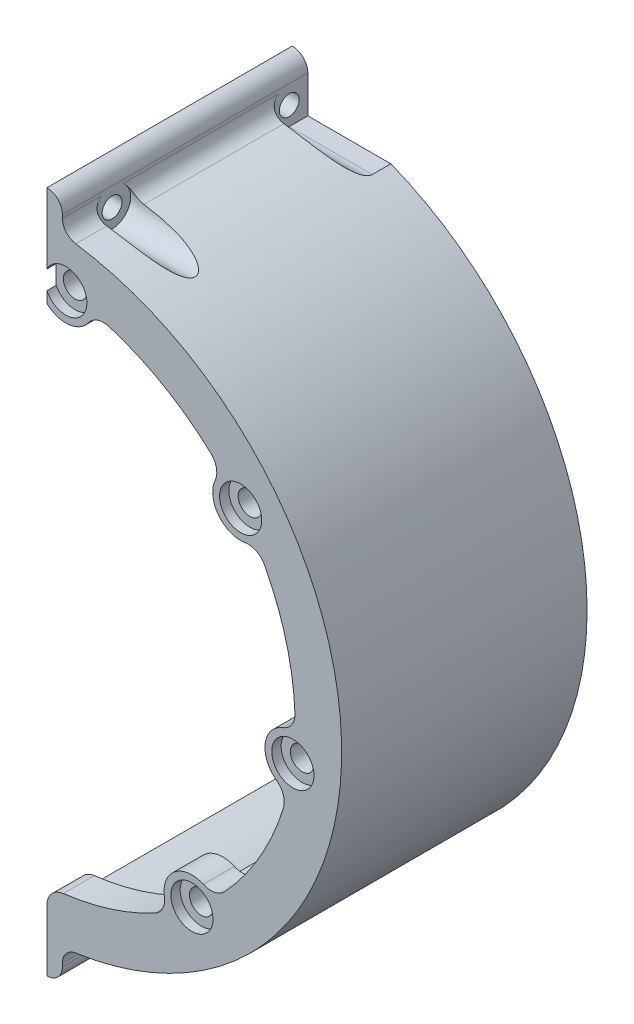
SolidWorks part; units mm, degrees
material "ABS"
ref_plane "前视基准面" through (0, 0, 0) normal (0, 0, 1) x (1, 0, 0)
ref_plane "上视基准面" through (0, 0, 0) normal (0, 1, 0) x (1, 0, 0)
ref_plane "右视基准面" through (0, 0, 0) normal (1, 0, 0) x (0, 0, -1)
sketch "草图1" plane through (0, 0, 0) normal (0, 0, 1) x (1, 0, 0)
  line L0 (0, 0) -> (0, 50)
  line L1 (0, 0) -> (0, -50)
  arc A0 (0, -50) -> (0, 50) centre (0, 0) ccw
extrude "凸台-拉伸1" add sketch "草图1" along normal blind 5
sketch "草图2" plane through (0, 0, 0) normal (0, 0, -1) x (-1, 0, 0)
  line L0 (0, 46) -> (0, 50)
  line L1 (0, -46) -> (0, -50)
  arc A0 (0, 50) -> (0, -50) centre (0, 0) ccw
  arc A1 (0, 46) -> (0, -46) centre (0, 0) ccw
extrude "凸台-拉伸2" add sketch "草图2" along normal blind 34.55
sketch "草图3" plane through (0, 0, 5) normal (0, 0, 1) x (1, 0, 0)
  line L1 (2.5, -50) -> (2.5, 50)
  line L2 (2.5, 50) -> (0, 50)
  line L3 (0, 50) -> (0, -50)
  line L4 (2.5, -50) -> (0, -50)
extrude "切除-拉伸1" cut sketch "草图3" against normal blind 41
sketch "草图4" plane through (0, 0, 5) normal (0, 0, 1) x (1, 0, 0)
  circle A0 centre (0, 0) radius 38
extrude "切除-拉伸2" cut sketch "草图4" against normal blind 5
sketch "草图5" plane through (0, 0, 5) normal (0, 0, 1) x (1, 0, 0)
  line L6 (2.75, 0) -> (-2.75, 0) construction
  line L7 (5, -52.5) -> (5, -51.9615)
  line L8 (2.5, 55) -> (2.5, 49.9375)
  line L9 (5, 52.5) -> (5, 51.9615)
  line L10 (2.5, -55) -> (2.5, -49.9375)
  line L12 (2.5, 49.9375) -> (7.1429, 49.4872)
  line L13 (2.5, -49.9375) -> (7.1429, -49.4872)
  arc A11 (5, 51.9615) -> (7.1429, 49.4872) centre (7.5, 51.9615) ccw
  arc A12 (5, 52.5) -> (2.5, 55) centre (2.5, 52.5) ccw
  arc A15 (5, -52.5) -> (2.5, -55) centre (2.5, -52.5) cw
  arc A16 (5, -51.9615) -> (7.1429, -49.4872) centre (7.5, -51.9615) cw
extrude "凸台-拉伸3" add sketch "草图5" against normal up to surface (39.55 mm away) up to face at (25.25, 0, -34.55)
sketch "草图6" plane through (0, 0, 5) normal (0, 0, 1) x (1, 0, 0)
  circle A1 centre (33.7175, 25.8724) radius 1.9
  circle A2 centre (5.5474, 42.1364) radius 1.9
  circle A8 centre (42.1364, -5.5474) radius 1.9
  circle A9 centre (25.8724, -33.7175) radius 1.9
  circle A10 centre (-5.5474, -42.1364) radius 1.9
  circle A11 centre (-33.7175, -25.8724) radius 1.9
  circle A12 centre (-42.1364, 5.5474) radius 1.9
  circle A13 centre (-25.8724, 33.7175) radius 1.9
  point P19 (0, 0)
  dimension "D1" = 8
extrude "切除-拉伸3" cut sketch "草图6" against normal blind 10
sketch "草图7" plane through (2.5, 0, 0) normal (-1, 0, 0) x (0, 0, 1)
  circle A0 centre (-3, 49.5) radius 1.6
  circle A1 centre (-31.55, 49.5) radius 1.6
  circle A2 centre (-31.55, -49.5) radius 1.6
  circle A3 centre (-3, -49.5) radius 1.6
extrude "切除-拉伸4" cut sketch "草图7" against normal through all
sketch "草图9" plane through (2.5, 0, 0) normal (-1, 0, 0) x (0, 0, 1)
  line L0 (-31.55, 52.5) -> (-34.55, 52.5)
  line L1 (-34.55, 55) -> (-34.55, 45.932) construction
  line L2 (-34.55, 52.5) -> (-34.55, 46.5)
  line L3 (-34.55, 46.5) -> (-31.55, 46.5)
  line L4 (-31.55, -46.5) -> (-34.55, -46.5)
  line L5 (-34.55, -45.932) -> (-34.55, -55) construction
  line L6 (-34.55, -46.5) -> (-34.55, -52.5)
  line L7 (-34.55, -52.5) -> (-31.55, -52.5)
  arc A0 (-31.55, 46.5) -> (-31.55, 52.5) centre (-31.55, 49.5) ccw
  circle A1 centre (-3, 49.5) radius 3
  circle A2 centre (-3, -49.5) radius 3
  arc A3 (-31.55, -52.5) -> (-31.55, -46.5) centre (-31.55, -49.5) ccw
extrude "切除-拉伸7" cut sketch "草图9" against normal through all from offset 2.5 offset against normal yes
sketch "草图11" plane through (0, 0, 0) normal (0, 0, -1) x (-1, 0, 0)
  arc A0 (-4.96, 37.6749) -> (-30.1474, 23.1329) centre (0, 0) ccw
  arc A1 (-30.1474, 23.1329) -> (-30.7929, 29.2924) centre (-33.7175, 25.8724) ccw
  arc A2 (-9.9715, 41.3137) -> (-4.96, 37.6749) centre (-5.5474, 42.1364) ccw
  arc A3 (-9.9715, 41.3137) -> (-30.7929, 29.2924) centre (0, 0) ccw
  arc A4 (-2.5, 37.9177) -> (-2.5, -37.9177) centre (0, 0) ccw construction
  circle A5 centre (-33.7175, 25.8724) radius 1.9 construction
  arc A6 (23.1329, 30.1474) -> (-4.96, 37.6749) centre (0, 0) ccw
  arc A7 (-4.96, 37.6749) -> (-1.061, 42.4868) centre (-5.5474, 42.1364) ccw
  arc A8 (22.1622, 36.2641) -> (23.1329, 30.1474) centre (25.8724, 33.7175) ccw
  arc A9 (22.1622, 36.2641) -> (-1.061, 42.4868) centre (0, 0) ccw
  arc A10 (37.6749, 4.96) -> (23.1329, 30.1474) centre (0, 0) ccw
  arc A11 (23.1329, 30.1474) -> (29.2924, 30.7929) centre (25.8724, 33.7175) ccw
  arc A12 (41.3137, 9.9715) -> (37.6749, 4.96) centre (42.1364, 5.5474) ccw
  arc A13 (41.3137, 9.9715) -> (29.2924, 30.7929) centre (0, 0) ccw
  arc A14 (30.1474, -23.1329) -> (37.6749, 4.96) centre (0, 0) ccw
  arc A15 (37.6749, 4.96) -> (42.4868, 1.061) centre (42.1364, 5.5474) ccw
  arc A16 (36.2641, -22.1622) -> (30.1474, -23.1329) centre (33.7175, -25.8724) ccw
  arc A17 (36.2641, -22.1622) -> (42.4868, 1.061) centre (0, 0) ccw
  arc A18 (4.96, -37.6749) -> (30.1474, -23.1329) centre (0, 0) ccw
  arc A19 (30.1474, -23.1329) -> (30.7929, -29.2924) centre (33.7175, -25.8724) ccw
  arc A20 (9.9715, -41.3137) -> (4.96, -37.6749) centre (5.5474, -42.1364) ccw
  arc A21 (9.9715, -41.3137) -> (30.7929, -29.2924) centre (0, 0) ccw
  arc A22 (-23.1329, -30.1474) -> (4.96, -37.6749) centre (0, 0) ccw
  arc A23 (4.96, -37.6749) -> (1.061, -42.4868) centre (5.5474, -42.1364) ccw
  arc A24 (-22.1622, -36.2641) -> (-23.1329, -30.1474) centre (-25.8724, -33.7175) ccw
  arc A25 (-22.1622, -36.2641) -> (1.061, -42.4868) centre (0, 0) ccw
  arc A26 (-37.6749, -4.96) -> (-23.1329, -30.1474) centre (0, 0) ccw
  arc A27 (-23.1329, -30.1474) -> (-29.2924, -30.7929) centre (-25.8724, -33.7175) ccw
  arc A28 (-41.3137, -9.9715) -> (-37.6749, -4.96) centre (-42.1364, -5.5474) ccw
  arc A29 (-41.3137, -9.9715) -> (-29.2924, -30.7929) centre (0, 0) ccw
  arc A30 (-30.1474, 23.1329) -> (-37.6749, -4.96) centre (0, 0) ccw
  arc A31 (-37.6749, -4.96) -> (-42.4868, -1.061) centre (-42.1364, -5.5474) ccw
  arc A32 (-36.2641, 22.1622) -> (-30.1474, 23.1329) centre (-33.7175, 25.8724) ccw
  arc A33 (-36.2641, 22.1622) -> (-42.4868, -1.061) centre (0, 0) ccw
  point P60 (0, 0)
  arc M10 (-2.5, -37.9177) -> (-2.5, 37.9177) centre (0, 0) cw
  line M14 (-2.5, -45.932) -> (-2.5, -37.9177)
  dimension "D1" = 8
extrude "切除-拉伸8" cut sketch "草图11" against normal blind 10 contours A2 A3 A1 M10 | A32 A33 A31 M10 | A28 A29 A27 M10 | A24 A25 M14 M10 | A6 A7 A9 A8
fillet "圆角1" radius 3 8 edges at (2.5, -42.4264, 2.5) (41.3137, -9.9715, 2.5) (29.2924, -30.7929, 2.5) (22.1622, -36.2641, 2.5) (36.2641, 22.1622, 2.5) (42.4868, -1.061, 2.5) (9.9715, 41.3137, 2.5) (30.7929, 29.2924, 2.5)
sketch "草图12" plane through (0, 0, -34.55) normal (0, 0, -1) x (-1, 0, 0)
  line L0 (-2.5, 43.5) -> (0, 0)
  line L1 (21.7525, 0) -> (-21.7525, 0) construction
  line L2 (-2.5, -43.5) -> (-20.2916, -43.5)
  line L3 (-2.5, -43.5) -> (0, 0)
  line L4 (-2.5, 43.5) -> (-20.2916, 43.5)
  arc A0 (-20.2916, 43.5) -> (-20.2916, -43.5) centre (0, 0) ccw
extrude "切除-拉伸9" cut sketch "草图12" against normal up to surface (34.55 mm away) up to face at (27.7724, -33.7175, 0)
sketch "草图13" plane through (0, 0, 5) normal (0, 0, 1) x (1, 0, 0)
  circle A0 centre (5.5474, 42.1364) radius 3.4
  circle A1 centre (33.7175, 25.8724) radius 3.4
  circle A2 centre (42.1364, -5.5474) radius 3.4
  circle A3 centre (25.8724, -33.7175) radius 3.4
extrude "切除-拉伸10" cut sketch "草图13" against normal blind 1.5
